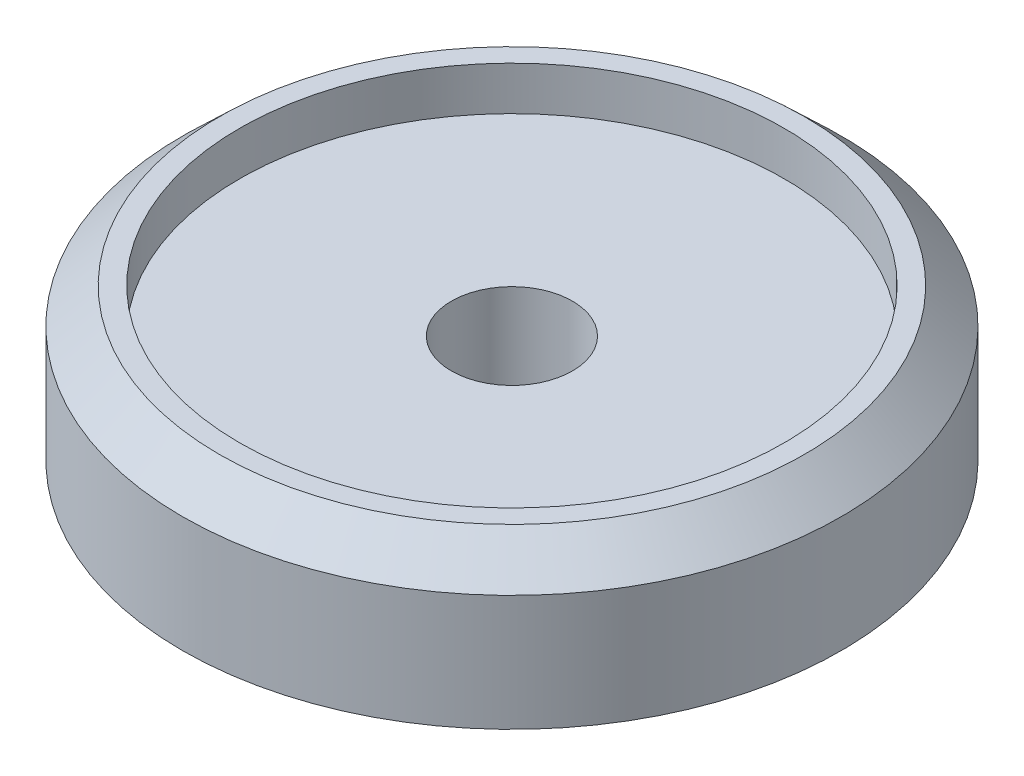
SolidWorks part; units mm, degrees
material "ABS"
ref_plane "Front Plane" through (0, 0, 0) normal (0, 0, 1) x (1, 0, 0)
ref_plane "Top Plane" through (0, 0, 0) normal (0, 1, 0) x (1, 0, 0)
ref_plane "Right Plane" through (0, 0, 0) normal (1, 0, 0) x (0, 0, -1)
sketch "Sketch1" plane through (0, 0, 0) normal (0, 1, 0) x (1, 0, 0)
  circle A0 centre (0, 0) radius 49
  dimension "D1" = 98
extrude "Boss-Extrude1" add sketch "Sketch1" along normal blind 16
sketch "Sketch2" plane through (0, 0, 0) normal (0, 0, 1) x (1, 0, 0)
  line L0 (-43.5, 22.5) -> (-40.5, 22.5)
  line L1 (49, 16) -> (-49, 16) construction
  line L3 (-43.5, 22.5) -> (-49, 17.25)
  line L4 (-49, 17.25) -> (-49, 16)
  line L5 (-49, 16) -> (-40.5, 16)
  line L6 (-40.5, 16) -> (-40.5, 22.5)
  dimension "D1" = 1.25
  dimension "D2" = 3
  dimension "D3" = 8.5
  dimension "D4" = 6.5
ref_axis "Axis1" through (0, 16, 0) along (0, -1, 0)
revolve "Revolve1" add sketch "Sketch2" angle 360 about axis through (0, 16, 0) along (0, -1, 0)
sketch "Sketch3" plane through (0, 0, 0) normal (0, -1, 0) x (1, 0, 0)
  circle A0 centre (0, 0) radius 12
  dimension "D1" = 24
extrude "Boss-Extrude2" add sketch "Sketch3" along normal blind 25
sketch "Sketch4" plane through (0, 16, 0) normal (0, 1, 0) x (1, 0, 0)
  circle A0 centre (0, 0) radius 9
  dimension "D1" = 18
extrude "Cut-Extrude1" cut sketch "Sketch4" against normal through all
